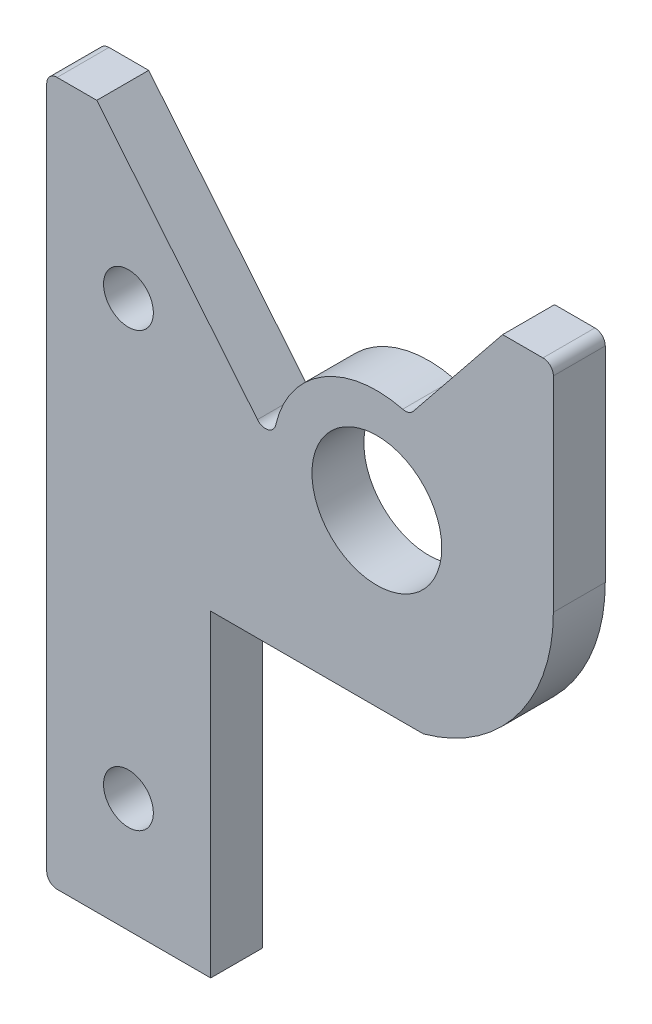
SolidWorks part; units mm, degrees
material "ASTM A36 Steel"
ref_plane "Front Plane" through (0, 0, 0) normal (0, 0, 1) x (1, 0, 0)
ref_plane "Top Plane" through (0, 0, 0) normal (0, 1, 0) x (1, 0, 0)
ref_plane "Right Plane" through (0, 0, 0) normal (1, 0, 0) x (0, 0, -1)
sketch "Sketch1" plane through (0, 0, 0) normal (0, 0, 1) x (1, 0, 0)
  line L3 (21.59, 25.0424) -> (21.59, 0)
  line L4 (0, -21.59) -> (-39.1074, -21.59)
  line L6 (-40.3774, -20.32) -> (-40.3774, 25.0424)
  line L7 (-39.1074, 26.3124) -> (-34.2539, 26.3124)
  line L8 (-34.2539, 26.3124) -> (-14.5989, 2.3182)
  line L9 (20.32, 26.3124) -> (15.384, 26.3124)
  line L10 (15.384, 26.3124) -> (4.4649, 12.7349)
  line L11 (-39.1074, -21.59) -> (-20.3191, -21.59)
  line L12 (-20.3191, -21.59) -> (-20.3191, -20.828)
  line L13 (-20.3191, -20.828) -> (5.6853, -20.828)
  line L14 (-40.3774, -20.32) -> (-40.3774, -58.42)
  line L15 (-39.1074, -59.69) -> (-20.3191, -59.69)
  line L16 (-20.3191, -59.69) -> (-20.3191, -21.59)
  circle A0 centre (0, 0) radius 19.05 construction
  circle A1 centre (0, 0) radius 7.9375
  arc A2 (-12.3786, 2.839) -> (3.1593, 12.3008) centre (0, 0) cw
  arc A5 (21.59, 0) -> (0, -21.59) centre (0, 0) cw
  arc A6 (-12.3786, 2.839) -> (-14.5989, 2.3182) centre (-13.6165, 3.1229) cw
  arc A9 (-40.3774, 25.0424) -> (-39.1074, 26.3124) centre (-39.1074, 25.0424) cw
  arc A10 (-39.1074, -21.59) -> (-40.3774, -20.32) centre (-39.1074, -20.32) cw
  arc A11 (3.1593, 12.3008) -> (4.4649, 12.7349) centre (3.4752, 13.5308) ccw
  arc A12 (21.59, 25.0424) -> (20.32, 26.3124) centre (20.32, 25.0424) ccw
  arc A13 (-40.3774, -58.42) -> (-39.1074, -59.69) centre (-39.1074, -58.42) ccw
  circle A14 centre (-30.3825, -45.72) radius 3.048
  circle A15 centre (-30.3825, 7.2624) radius 3.048
  point P22 (-12.7, 0)
  dimension "D1" = 38.1
  dimension "D2" = 15.875
  dimension "D3" = 21.59
  dimension "D4" = 12.7
  dimension "D5" = 1.27
  dimension "D6" = 1.27
  dimension "D7" = 18.7884
  dimension "D10" = 1.27
  dimension "D11" = 6.096
  dimension "D14" = 6.096
  dimension "D8" = 0.762
  dimension "D9" = 38.1
  dimension "D12" = 9.9949
  dimension "D13" = 13.97
  dimension "D15" = 19.05
  dimension "D16" = 9.9949
extrude "Boss-Extrude1" add sketch "Sketch1" along normal blind 6.35 contours L3 A12 L9 L10 A11 A2 A6 L8 L7 A9 L6 A10 L4 L12 L13 A5 A1 | L14 A13 L15 L16 L4 A10
